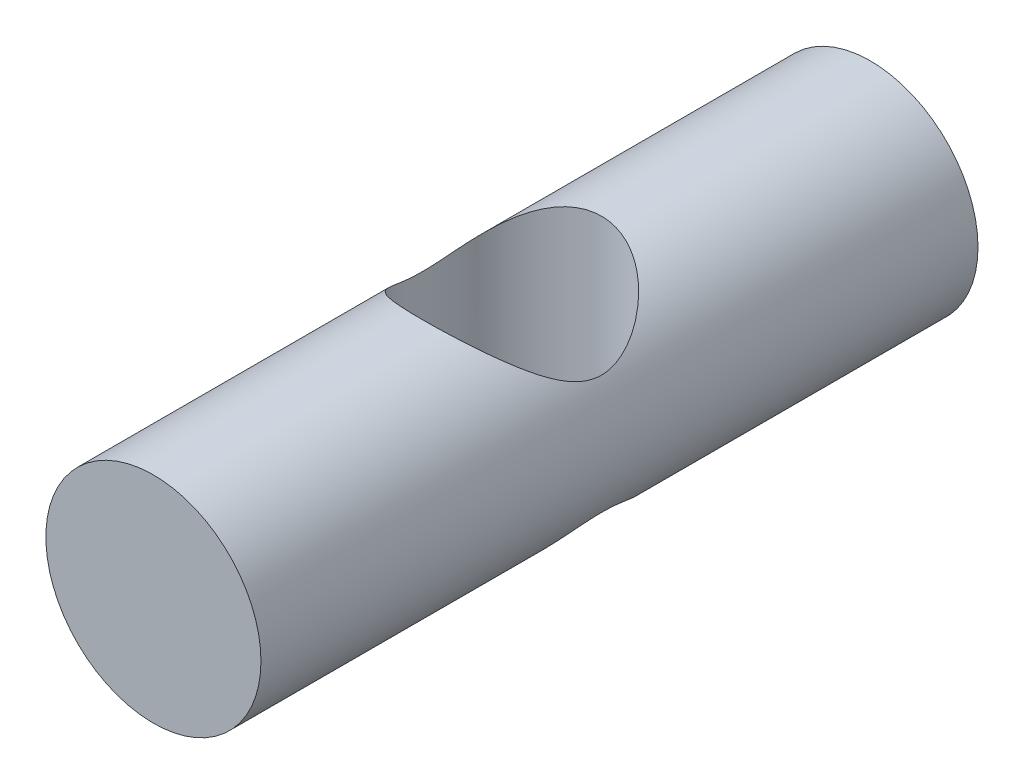
SolidWorks part; units mm, degrees
ref_plane "前视基准面" through (0, 0, 0) normal (0, 0, 1) x (1, 0, 0)
ref_plane "上视基准面" through (0, 0, 0) normal (0, 1, 0) x (1, 0, 0)
ref_plane "右视基准面" through (0, 0, 0) normal (1, 0, 0) x (0, 0, -1)
sketch "草图1" plane through (0, 0, 0) normal (0, 0, 1) x (1, 0, 0)
  circle A0 centre (0, 0) radius 6
  dimension "D1" = 12
extrude "凸台-拉伸1" add sketch "草图1" along normal mid plane 40
ref_plane "基准面1" through (0, 6, 0) normal (0, 1, 0) x (1, 0, 0)
sketch "草图3" plane through (0, 6, 0) normal (0, 1, 0) x (1, 0, 0)
  circle A0 centre (0, 0) radius 5
  dimension "D1" = 10
extrude "切除-拉伸1" cut sketch "草图3" against normal through all
